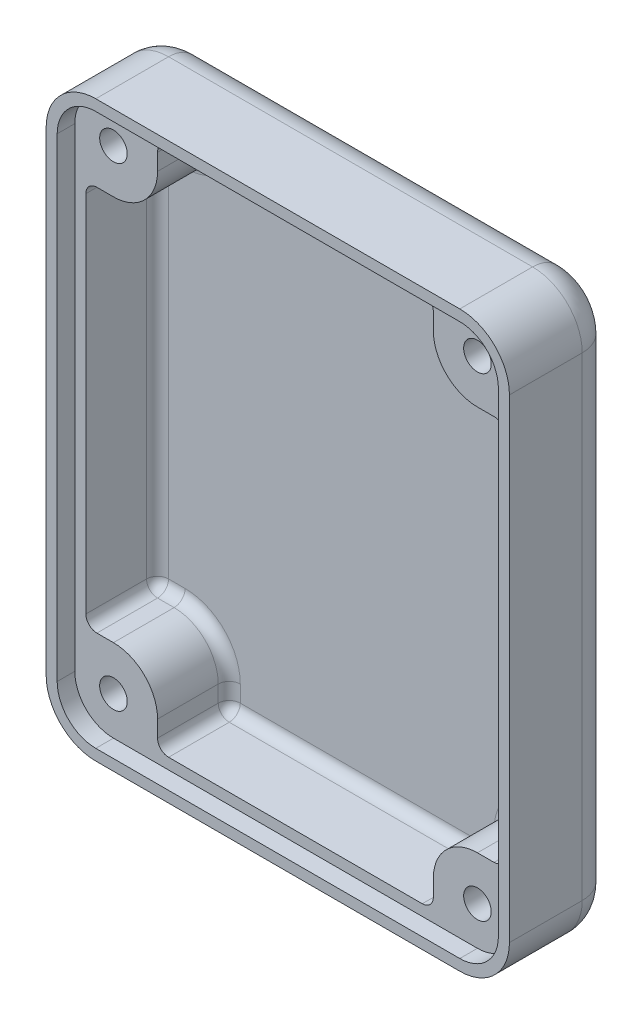
SolidWorks part; units mm, degrees
ref_plane "Front Plane" through (0, 0, 0) normal (0, 0, 1) x (1, 0, 0)
ref_plane "Top Plane" through (0, 0, 0) normal (0, 1, 0) x (1, 0, 0)
ref_plane "Right Plane" through (0, 0, 0) normal (1, 0, 0) x (0, 0, -1)
sketch "Sketch2" plane through (0, 0, 0) normal (0, 0, 1) x (1, 0, 0)
  line L0 (21, 21.5) -> (21, -21.5)
  line L9 (-16.5, -21.5) -> (16.5, 21.5) construction
  line L10 (-16.5, 21.5) -> (16.5, -21.5) construction
  line L11 (-16.5, -26) -> (16.5, -26)
  line L12 (-21, 21.5) -> (-21, -21.5)
  line L13 (-16.5, 26) -> (16.5, 26)
  arc A4 (21, 21.5) -> (16.5, 26) centre (16.5, 21.5) ccw
  arc A5 (-16.5, 26) -> (-21, 21.5) centre (-16.5, 21.5) ccw
  arc A6 (16.5, -26) -> (21, -21.5) centre (16.5, -21.5) ccw
  arc A7 (-21, -21.5) -> (-16.5, -26) centre (-16.5, -21.5) ccw
  point P0 (0, 0)
  dimension "D1" = 52
  dimension "D3" = 9
  dimension "D4" = 9
  dimension "D5" = 9
  dimension "D6" = 9
  dimension "D2" = 42
extrude "Boss-Extrude1" add sketch "Sketch2" along normal blind 9.6
sketch "Sketch3" plane through (0, 0, 0) normal (0, 0, 1) x (1, 0, 0)
  line L0 (-20, 21.5) -> (-20, -21.5)
  line L9 (-16.5, -21.5) -> (16.5, 21.5) construction
  line L10 (-16.5, 21.5) -> (16.5, -21.5) construction
  line L11 (-16.5, -25) -> (16.5, -25)
  line L12 (-16.5, 25) -> (16.5, 25)
  line L13 (20, 21.5) -> (20, -21.5)
  arc A4 (20, 21.5) -> (16.5, 25) centre (16.5, 21.5) ccw
  arc A5 (-16.5, 25) -> (-20, 21.5) centre (-16.5, 21.5) ccw
  arc A6 (16.5, -25) -> (20, -21.5) centre (16.5, -21.5) ccw
  arc A7 (-20, -21.5) -> (-16.5, -25) centre (-16.5, -21.5) ccw
  point P0 (0, 0)
  dimension "D1" = 50
  dimension "D2" = 40
extrude "Cut-Extrude1" cut sketch "Sketch3" against normal blind 1.6 from offset 9.6
sketch "Sketch4" plane through (0, 0, 0) normal (0, 0, 1) x (1, 0, 0)
  line L0 (-12.5, -21.5) -> (-12.5, -24)
  line L1 (-12.5, -24) -> (12.5, -24)
  line L3 (-12.5, 24) -> (12.5, 24)
  line L4 (19, -17.5) -> (19, 17.5)
  line L5 (-19, -24) -> (19, 24) construction
  line L6 (-19, 24) -> (19, -24) construction
  line L11 (-16.5, -21.5) -> (16.5, 21.5) construction
  line L12 (-16.5, 21.5) -> (16.5, -21.5) construction
  line L13 (-16.5, -17.5) -> (-19, -17.5)
  line L14 (-19, -17.5) -> (-19, 17.5)
  line L15 (12.5, -21.5) -> (12.5, -24)
  line L16 (16.5, -17.5) -> (19, -17.5)
  line L17 (-16.5, 17.5) -> (-19, 17.5)
  line L18 (-12.5, 21.5) -> (-12.5, 24)
  line L19 (12.5, 21.5) -> (12.5, 24)
  line L20 (16.5, 17.5) -> (19, 17.5)
  arc A0 (-16.5, 17.5) -> (-12.5, 21.5) centre (-16.5, 21.5) ccw
  arc A1 (12.5, 21.5) -> (16.5, 17.5) centre (16.5, 21.5) ccw
  arc A2 (-12.5, -21.5) -> (-16.5, -17.5) centre (-16.5, -21.5) ccw
  arc A3 (16.5, -17.5) -> (12.5, -21.5) centre (16.5, -21.5) ccw
  point P0 (0, 0)
  point P6 (0, 0)
extrude "Cut-Extrude2" cut sketch "Sketch4" against normal blind 8.1 from offset 9.6
sketch "Sketch5" plane through (0, 0, 0) normal (0, 0, 1) x (1, 0, 0)
  line L5 (-16.5, -21.5) -> (16.5, 21.5) construction
  line L6 (-16.5, 21.5) -> (16.5, -21.5) construction
  circle A0 centre (-16.5, 21.5) radius 1.25
  circle A1 centre (16.5, 21.5) radius 1.25
  circle A2 centre (-16.5, -21.5) radius 1.25
  circle A3 centre (16.5, -21.5) radius 1.25
  point P0 (0, 0)
extrude "Cut-Extrude3" cut sketch "Sketch5" against normal blind 8.1 from offset 9.6
fillet "Fillet2" radius 1 24 edges at (-17.75, -17.5, 1.5) (-12.5, -22.75, 1.5) (12.5, -22.75, 1.5) (17.75, -17.5, 1.5) (17.75, 17.5, 1.5) (12.5, 22.75, 1.5) (-12.5, 22.75, 1.5) (-17.75, 17.5, 1.5) (-12.5, 24, 4.75) (-19, 17.5, 4.75) (-19, -17.5, 4.75) (-12.5, -24, 4.75) (-13.6716, -18.6716, 1.5) (0, -24, 1.5) (12.5, -24, 4.75) (13.6716, -18.6716, 1.5) (19, -17.5, 4.75) (19, 0, 1.5) (19, 17.5, 4.75) (13.6716, 18.6716, 1.5) (12.5, 24, 4.75) (0, 24, 1.5) (-13.6716, 18.6716, 1.5) (-19, 0, 1.5)
fillet "Fillet3" radius 3 8 edges at (-19.682, -24.682, 0) (-21, 0, 0) (-19.682, 24.682, 0) (0, 26, 0) (19.682, 24.682, 0) (21, 0, 0) (19.682, -24.682, 0) (0, -26, 0)
